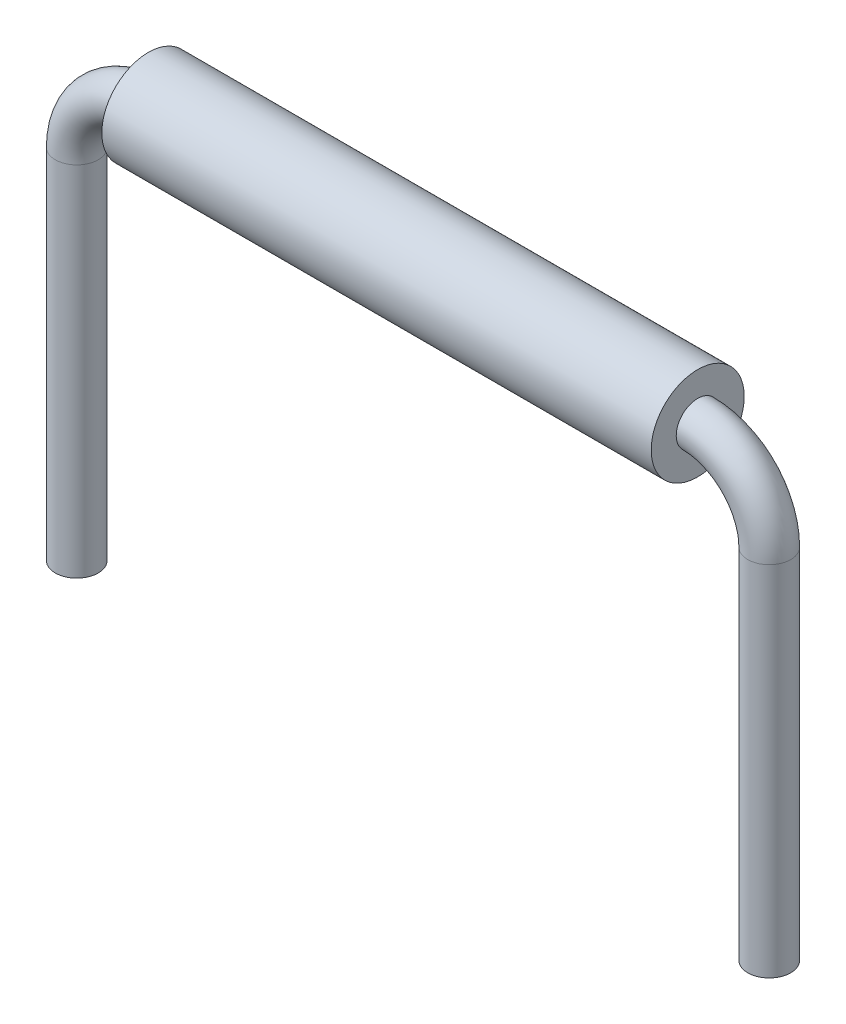
SolidWorks part; units mm, degrees
other "Wire"
other "Insulation"
ref_plane "Front Plane" through (0, 0, 0) normal (0, 0, 1) x (1, 0, 0)
ref_plane "Top Plane" through (0, 0, 0) normal (0, 1, 0) x (1, 0, 0)
ref_plane "Right Plane" through (0, 0, 0) normal (1, 0, 0) x (0, 0, -1)
sketch "Sketch1" plane through (0, 0, 0) normal (0, 0, 1) x (1, 0, 0)
  line L0 (-3.8375, 0) -> (3.8375, 0)
  line L1 (-4.8375, -1) -> (-4.8375, -6)
  line L2 (4.8375, -1) -> (4.8375, -6)
  line L3 (0, 0) -> (0, -6) construction
  line L4 (-4.8375, -6) -> (4.8375, -6) construction
  arc A0 (-3.8375, 0) -> (-4.8375, -1) centre (-3.8375, -1) ccw
  arc A1 (3.8375, 0) -> (4.8375, -1) centre (3.8375, -1) cw
  dimension "D1" = 1
  dimension "D2" = 9.675
  dimension "D3" = 6
sketch "Sketch2" plane through (0, 0, 0) normal (1, 0, 0) x (0, 0, -1)
  circle A0 centre (0, 0) radius 0.3
  dimension "D1" = 0.6
sweep "Sweep1" add profiles "Sketch2" path "Sketch1"
sketch "Sketch3" plane through (0, 0, 0) normal (1, 0, 0) x (0, 0, -1)
  circle A0 centre (0, 0) radius 0.65
  circle A1 centre (0, 0) radius 0.3
  dimension "D1" = 1.3
  dimension "D2" = 0.6
extrude "Boss-Extrude1" add sketch "Sketch3" along normal up to vertex (3.8375 mm away) and the other way up to vertex (3.8375 mm away) separate body up to point (3.8375, 0, 0) other way up to point (-3.8375, 0, 0)
